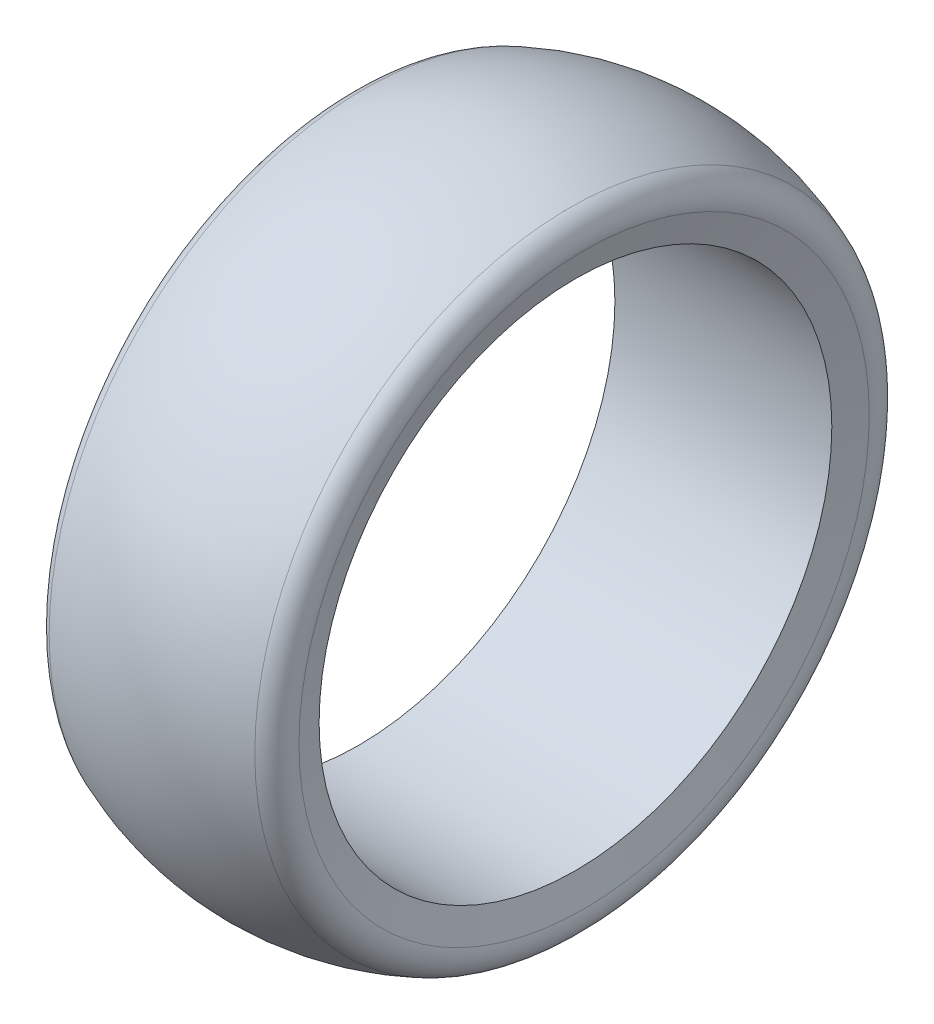
SolidWorks part; units mm, degrees
ref_plane "Plano frontal" through (0, 0, 0) normal (0, 0, 1) x (1, 0, 0)
ref_plane "Plano superior" through (0, 0, 0) normal (0, 1, 0) x (1, 0, 0)
ref_plane "Plano direito" through (0, 0, 0) normal (1, 0, 0) x (0, 0, -1)
sketch "Esboço2" plane through (0, 0, 0) normal (0, 0, 1) x (1, 0, 0)
  line L0 (0, 0) -> (29.1516, 0) construction
  line L1 (0, 31) -> (25, 31) construction
  line L2 (0, 26) -> (25, 26) construction
  line L3 (0, 26) -> (0, 34) construction
  line L4 (0, 34) -> (25, 34) construction
  line L5 (25, 26) -> (25, 34) construction
  line L9 (25, 31) -> (23.5, 26)
  line L10 (0, 31) -> (1.5, 26)
  line L11 (1.5, 26) -> (23.5, 26)
  arc A0 (0, 31) -> (25, 31) centre (12.5, 6.4583) cw
  dimension "D1" = 34
  dimension "D2" = 25
  dimension "D3" = 8
  dimension "D4" = 3
  dimension "D5" = 1.5
  dimension "D6" = 1.5
revolve "Revolução1" add sketch "Esboço2" angle 360 about L0
fillet "Filete1" radius 2.5 2 edges at (0, 0, 31) (25, 0, 31)
